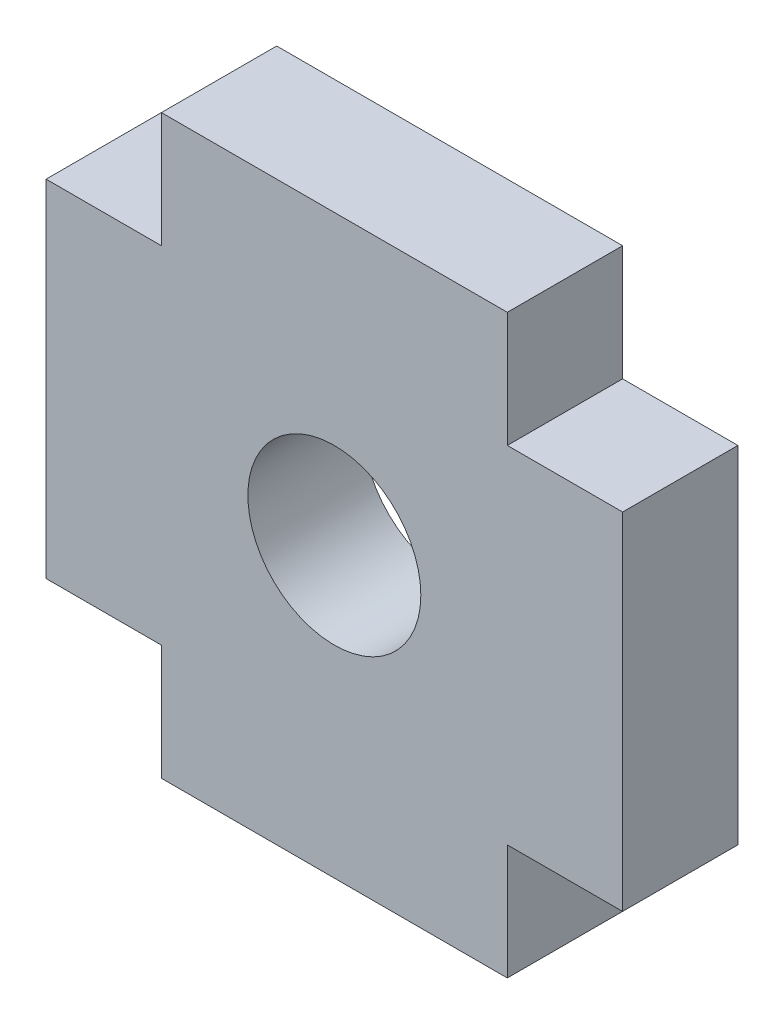
SolidWorks part; units mm, degrees
material "Acrylic (Medium-high impact)"
ref_plane "Front Plane" through (0, 0, 0) normal (0, 0, 1) x (1, 0, 0)
ref_plane "Top Plane" through (0, 0, 0) normal (0, 1, 0) x (1, 0, 0)
ref_plane "Right Plane" through (0, 0, 0) normal (1, 0, 0) x (0, 0, -1)
sketch "Model" plane through (0, 0, 0) normal (0, 0, 1) x (1, 0, 0)
  line L239 (-5, -3) -> (-3, -3)
  line L240 (-3, -3) -> (-3, -5)
  line L241 (-3, -5) -> (3, -5)
  line L242 (3, -5) -> (3, -3)
  line L243 (3, 3) -> (3, 5)
  line L244 (3, 5) -> (-3, 5)
  line L245 (-3, 5) -> (-3, 3)
  line L246 (-3, 3) -> (-5, 3)
  line L247 (-5, 3) -> (-5, -3)
  line L248 (3, 3) -> (5, 3)
  line L249 (5, 3) -> (5, -3)
  line L250 (5, -3) -> (3, -3)
  circle A104 centre (0, 0) radius 1.5
  dimension "D1" = 3
  dimension "D2" = 3
  dimension "D3" = 5
  dimension "D4" = 3
  dimension "D5" = 3
extrude "Boss-Extrude1" add sketch "Model" along normal blind 2
